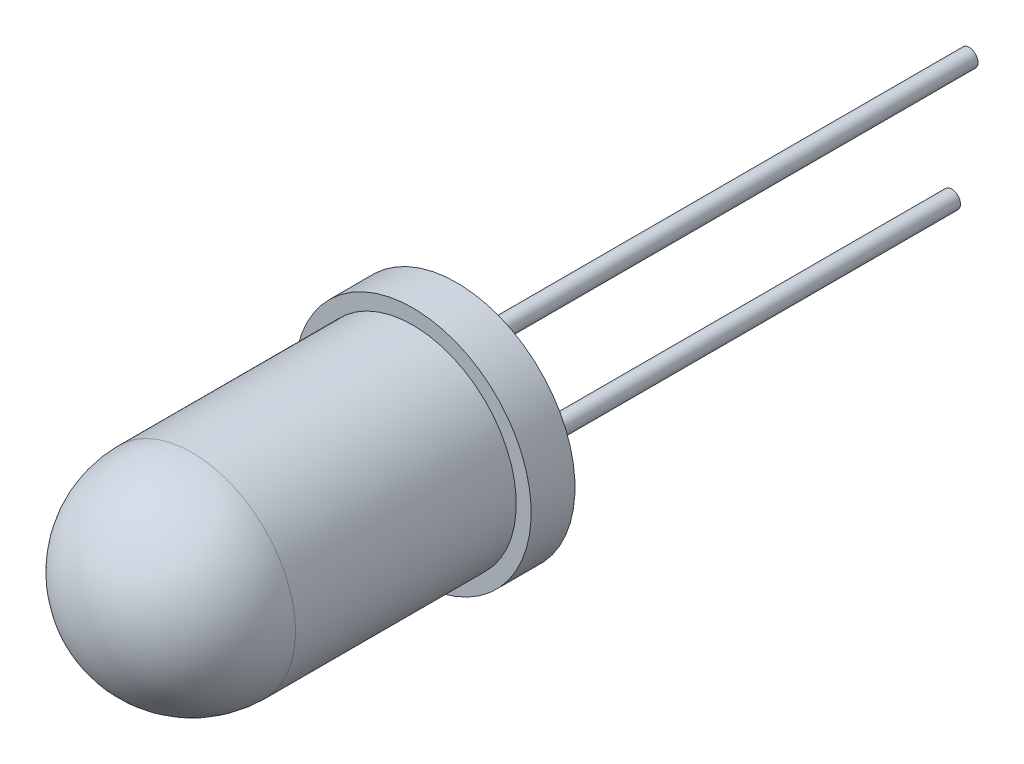
SolidWorks part; units mm, degrees
material "铍红铜, UNS C17000"
ref_plane "前视基准面" through (0, 0, 0) normal (0, 0, 1) x (1, 0, 0)
ref_plane "上视基准面" through (0, 0, 0) normal (0, 1, 0) x (1, 0, 0)
ref_plane "右视基准面" through (0, 0, 0) normal (1, 0, 0) x (0, 0, -1)
sketch "草图2" plane through (0, 0, 0) normal (0, 1, 0) x (1, 0, 0)
  line L0 (0, 0) -> (0, -19.4676) construction
  line L1 (2.36, -6.04) -> (2.36, -1)
  line L4 (2.36, -1) -> (2.7, -1)
  line L5 (2.7, -1) -> (2.7, 0)
  line L6 (2.7, 0) -> (0, 0)
  line L7 (0, 0) -> (0, -8.4)
  arc A2 (0, -8.4) -> (2.36, -6.04) centre (0, -6.04) ccw
  point P7 (2.53, -1)
  dimension "D1" = 4.72
  dimension "D4" = 8.4
  dimension "D2" = 5.4
  dimension "D3" = 1
revolve "旋转1" add sketch "草图2" angle 360 about L0
sketch "草图3" plane through (0, 0, 0) normal (0, 0, -1) x (-1, 0, 0)
  line L0 (2.3022, 0) -> (-2.2678, 0) construction
  circle A0 centre (1.3, 0) radius 0.2
  circle A1 centre (-1.3, 0) radius 0.2
  dimension "D1" = 0.4
  dimension "D2" = 0.4
  dimension "D3" = 1.3
  dimension "D4" = 1.3
extrude "凸台-拉伸1" add sketch "草图3" along normal blind 10
sketch "草图4" plane through (0, 0, -10) normal (0, 0, -1) x (-1, 0, 0)
  circle A1 centre (1.3, 0) radius 0.2
  circle A2 centre (1.3, 0) radius 0.2
  dimension "D1" = 0
extrude "凸台-拉伸2" add sketch "草图4" along normal blind 3
